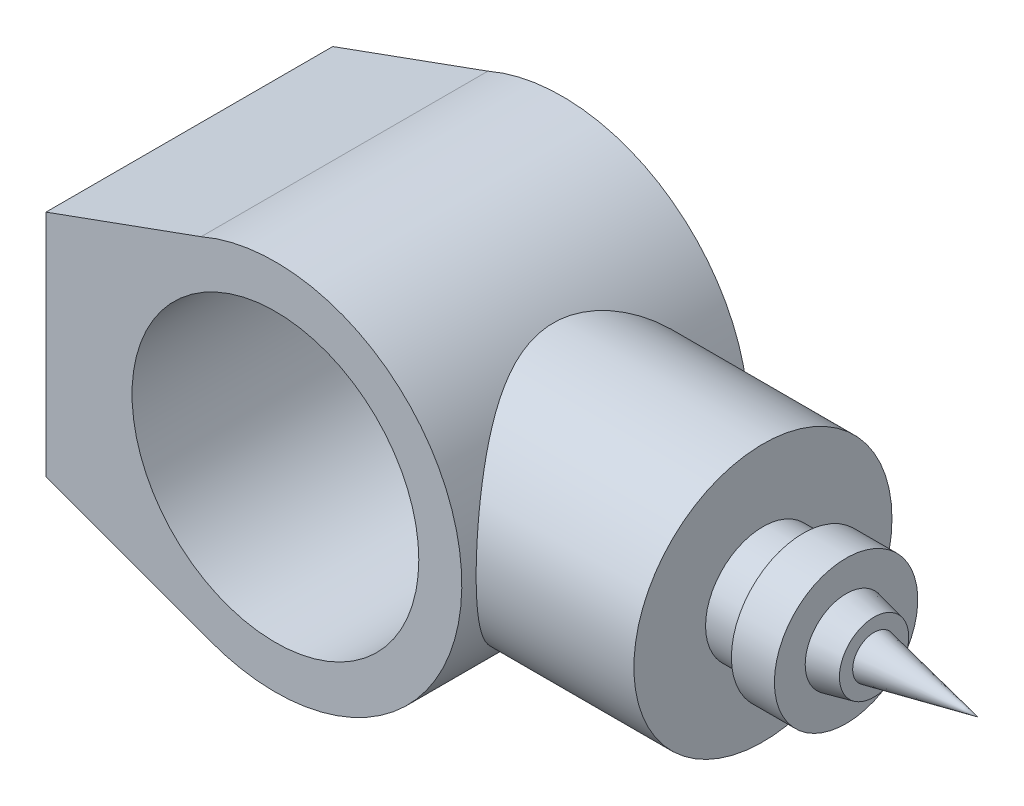
SolidWorks part; units mm, degrees
ref_plane "Front Plane" through (0, 0, 0) normal (0, 0, 1) x (1, 0, 0)
ref_plane "Top Plane" through (0, 0, 0) normal (0, 1, 0) x (1, 0, 0)
ref_plane "Right Plane" through (0, 0, 0) normal (1, 0, 0) x (0, 0, -1)
sketch "Sketch1" plane through (0, 0, 0) normal (0, 0, 1) x (1, 0, 0)
  line L0 (0, 0) -> (-80, 0) construction
  line L1 (-80, -40) -> (-80, 40)
  line L2 (-80, 40) -> (-25.9122, 59.6117)
  line L3 (-80, -40) -> (-22.9381, -60.8181)
  arc A0 (-22.9381, -60.8181) -> (-25.9122, 59.6117) centre (0, 0) ccw
  circle A1 centre (0, 0) radius 50
  point P8 (-80, 0)
  dimension "D1" = 100
  dimension "D2" = 65
  dimension "D3" = 22.9381
  dimension "D4" = 25.9122
  dimension "D5" = 80
extrude "Boss-Extrude1" add sketch "Sketch1" along normal mid plane 100
ref_plane "Plane1" through (120, 0, 0) normal (1, 0, 0) x (0, 0, -1)
sketch "Sketch2" plane through (120, 0, 0) normal (1, 0, 0) x (0, 0, -1)
  circle A0 centre (0, 0) radius 45
  dimension "D1" = 90
extrude "Boss-Extrude2" add sketch "Sketch2" against normal up to next
sketch "Sketch4" plane through (0, 0, 0) normal (0, 1, 0) x (1, 0, 0)
  line L0 (0, 0) -> (120, 0) construction
  line L1 (120, -55) -> (120, 55) construction
  line L2 (120, 0) -> (195, 0)
  line L3 (120, 0) -> (120, -20)
  line L4 (120, -20) -> (134, -20)
  line L5 (134, -20) -> (134, -25)
  line L6 (134, -25) -> (149, -25)
  line L7 (149, -25) -> (149, -14.2566)
  line L8 (149, -14.2566) -> (158.761, -12.0835)
  line L9 (158.761, -12.0835) -> (158.761, -7.4657)
  line L10 (158.761, -7.4657) -> (195, 0)
  dimension "D1" = 134
  dimension "D2" = 149
  dimension "D3" = 158.761
  dimension "D4" = 195
  dimension "D5" = 7.4657
  dimension "D6" = 12.0835
  dimension "D7" = 14.2566
  dimension "D8" = 20
  dimension "D9" = 25
revolve "Revolve2" add sketch "Sketch4" angle 360 about L0
